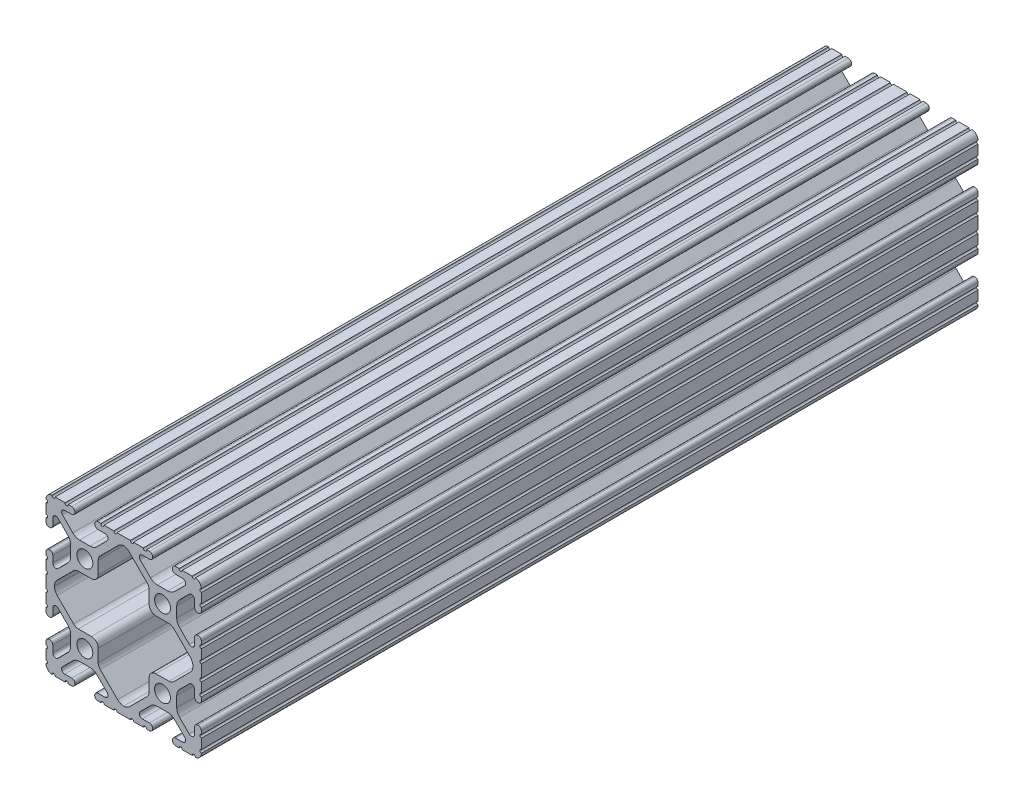
SolidWorks part; units mm, degrees
material "6061 Alloy"
ref_plane "Front Plane" through (0, 0, 0) normal (0, 0, 1) x (1, 0, 0)
ref_plane "Top Plane" through (0, 0, 0) normal (0, 1, 0) x (1, 0, 0)
ref_plane "Right Plane" through (0, 0, 0) normal (1, 0, 0) x (0, 0, -1)
sketch "Sketch1" plane through (0, 0, 0) normal (0, 0, 1) x (1, 0, 0)
  line L1 (-2.2101, -25.4) -> (2.2101, -25.4)
  line L2 (12.7883, 29.5847) -> (12.7883, -24.0404) construction
  line L3 (7.4579, -25.4) -> (8.4051, -25.4)
  line L4 (9.4615, -24.3587) -> (9.4615, -24.2315)
  line L5 (6.0878, -23.1902) -> (8.4051, -23.1902)
  line L6 (-12.7, -45.1098) -> (-12.7, 28.7522) construction
  line L7 (-25.8162, -12.7) -> (-12.7, -12.7) construction
  line L8 (0, 25.5922) -> (0, -25.5922) construction
  line L9 (-22.8238, 0) -> (0, 0) construction
  line L10 (8.763, -18.1257) -> (5.388, -21.5008)
  line L11 (14.3919, -17.1958) -> (11.0081, -17.1958)
  line L12 (20.012, -21.5008) -> (16.637, -18.1257)
  line L13 (16.9799, -23.1901) -> (19.2977, -23.1901)
  line L14 (15.9385, -24.3585) -> (15.9385, -24.2315)
  line L15 (16.9949, -25.4) -> (18.134, -25.4)
  line L16 (19.1384, -25.4) -> (20.1295, -25.4)
  line L17 (20.1295, -25.4) -> (22.4132, -25.4)
  line L18 (23.4501, -25.4) -> (23.4176, -25.4)
  line L19 (25.4, -23.294) -> (25.4, -23.2686)
  line L20 (25.4, -22.2526) -> (25.4, -21.1604)
  line L21 (25.4, -21.1604) -> (25.4, -19.0252)
  line L22 (25.4, -18.0092) -> (25.4, -16.916)
  line L23 (24.2316, -15.8746) -> (24.3586, -15.8746)
  line L24 (23.1902, -19.101) -> (23.1902, -16.916)
  line L25 (18.2781, -16.6418) -> (21.4558, -19.8194)
  line L26 (17.3482, -11.0035) -> (17.3482, -14.3967)
  line L27 (21.4566, -5.5875) -> (18.2808, -8.7557)
  line L28 (23.1902, -8.484) -> (23.1902, -6.3068)
  line L29 (-1.9878, -21.7759) -> (-7.684, -16.0797)
  line L30 (10.541, 8.1792) -> (14.8161, 8.1792)
  line L31 (-16.3772, -7.5334) -> (-21.7734, -2.1502)
  line L32 (24.3586, -9.5254) -> (24.2316, -9.5254)
  line L33 (25.4, -8.484) -> (25.4, -7.3277)
  line L34 (25.4, -3.0843) -> (25.4, -6.3117)
  line L35 (-25.4, 6.3117) -> (-25.4, 3.0843)
  line L36 (-22.6314, 0.0822) -> (-22.6314, -0.0822)
  line L37 (16.3772, -7.5334) -> (21.7734, -2.1502)
  line L38 (-14.8165, -8.1788) -> (-10.541, -8.1788)
  line L39 (12.7, -12.7) -> (25.8162, -12.7) construction
  line L40 (1.9878, -21.7759) -> (7.684, -16.0797)
  line L41 (3.2145, -25.4) -> (6.4535, -25.4)
  line L42 (22.6314, 0.0822) -> (22.6314, -0.0822)
  line L43 (-17.3482, -11.0035) -> (-17.3482, -14.3967)
  line L44 (25.4, 6.3117) -> (25.4, 3.0843)
  line L45 (-23.4501, -25.4) -> (-23.4176, -25.4)
  line L46 (-5.2705, 25.4) -> (-3.2145, 25.4)
  line L47 (-6.4535, 25.4) -> (-5.2705, 25.4)
  line L48 (-8.4051, 25.4) -> (-7.4579, 25.4)
  line L49 (-9.4615, 24.2315) -> (-9.4615, 24.3587)
  line L50 (-8.4051, 23.1902) -> (-6.0878, 23.1902)
  line L51 (-8.763, 18.1257) -> (-5.388, 21.5008)
  line L52 (-14.3919, 17.1958) -> (-11.0081, 17.1958)
  line L53 (-20.012, 21.5008) -> (-16.637, 18.1257)
  line L54 (-19.2977, 23.1901) -> (-16.9799, 23.1901)
  line L55 (-15.9385, 24.3585) -> (-15.9385, 24.2315)
  line L56 (-18.134, 25.4) -> (-16.9949, 25.4)
  line L57 (-20.1295, 25.4) -> (-19.1384, 25.4)
  line L58 (-22.4132, 25.4) -> (-20.1295, 25.4)
  line L59 (-23.4501, 25.4) -> (-23.4176, 25.4)
  line L60 (-25.4, 23.2686) -> (-25.4, 23.294)
  line L61 (-25.4, 21.1604) -> (-25.4, 22.2526)
  line L62 (-25.4, 19.0252) -> (-25.4, 21.1604)
  line L63 (-25.4, 16.916) -> (-25.4, 18.0092)
  line L64 (-24.3586, 15.8746) -> (-24.2316, 15.8746)
  line L65 (-23.1902, 19.101) -> (-23.1902, 16.916)
  line L66 (-18.2781, 16.6418) -> (-21.4558, 19.8194)
  line L67 (-17.3482, 11.0035) -> (-17.3482, 14.3967)
  line L68 (-21.4566, 5.5875) -> (-18.2808, 8.7557)
  line L69 (-23.1902, 6.3068) -> (-23.1902, 8.484)
  line L70 (-24.3586, 9.5254) -> (-24.2316, 9.5254)
  line L71 (-25.4, 7.3277) -> (-25.4, 8.484)
  line L74 (-14.8165, 8.1788) -> (-10.541, 8.1788)
  line L75 (-8.3312, 10.3886) -> (-8.3312, 14.5171)
  line L76 (3.2145, 25.4) -> (6.4535, 25.4)
  line L77 (1.7956, 21.9681) -> (7.684, 16.0797)
  line L78 (12.7, 12.7) -> (25.8162, 12.7) construction
  line L80 (16.3768, 7.5339) -> (21.7734, 2.1502)
  line L82 (25.4, 2.0683) -> (25.4, -2.0683)
  line L83 (8.3312, 12.7001) -> (8.3312, 10.389)
  line L84 (25.4, 7.3277) -> (25.4, 8.484)
  line L85 (24.3586, 9.5254) -> (24.2316, 9.5254)
  line L86 (-16.3772, 7.5334) -> (-21.7734, 2.1502)
  line L88 (-1.7956, 21.9681) -> (-7.684, 16.0797)
  line L89 (23.1902, 6.3068) -> (23.1902, 8.484)
  line L90 (21.4566, 5.5875) -> (18.2808, 8.7557)
  line L91 (17.3482, 11.0035) -> (17.3482, 14.3967)
  line L92 (18.2781, 16.6418) -> (21.4558, 19.8194)
  line L93 (23.1902, 19.101) -> (23.1902, 16.916)
  line L94 (24.2316, 15.8746) -> (24.3586, 15.8746)
  line L95 (25.4, 16.916) -> (25.4, 18.0092)
  line L96 (25.4, 19.0252) -> (25.4, 21.1604)
  line L97 (25.4, 21.1604) -> (25.4, 22.2526)
  line L98 (25.4, 23.2686) -> (25.4, 23.294)
  line L99 (23.4501, 25.4) -> (23.4176, 25.4)
  line L100 (20.1295, 25.4) -> (22.4132, 25.4)
  line L101 (19.1384, 25.4) -> (20.1295, 25.4)
  line L102 (16.9949, 25.4) -> (18.134, 25.4)
  line L103 (15.9385, 24.3585) -> (15.9385, 24.2315)
  line L104 (16.9799, 23.1901) -> (19.2977, 23.1901)
  line L105 (20.012, 21.5008) -> (16.637, 18.1257)
  line L106 (14.3919, 17.1958) -> (11.0081, 17.1958)
  line L107 (8.763, 18.1257) -> (5.388, 21.5008)
  line L108 (-25.8162, 12.7) -> (-12.7, 12.7) construction
  line L109 (6.0878, 23.1902) -> (8.4051, 23.1902)
  line L110 (9.4615, 24.2315) -> (9.4615, 24.3587)
  line L111 (7.4579, 25.4) -> (8.4051, 25.4)
  line L112 (8.3312, 12.7001) -> (8.3312, 14.5171)
  line L113 (-2.2101, 25.4) -> (2.2101, 25.4)
  line L114 (-22.4132, -25.4) -> (-20.1295, -25.4)
  line L115 (-20.1295, -25.4) -> (-19.1384, -25.4)
  line L116 (-18.134, -25.4) -> (-16.9949, -25.4)
  line L117 (-8.4051, -25.4) -> (-7.4579, -25.4)
  line L118 (-6.4535, -25.4) -> (-5.2705, -25.4)
  line L119 (-5.2705, -25.4) -> (-3.2145, -25.4)
  line L120 (-19.2977, -23.1901) -> (-16.9799, -23.1901)
  line L121 (-8.4051, -23.1902) -> (-6.0878, -23.1902)
  line L122 (-8.3312, -14.5171) -> (-8.3312, -10.3886)
  line L123 (-14.3919, -17.1958) -> (-11.0081, -17.1958)
  line L125 (-24.3586, -15.8746) -> (-24.2316, -15.8746)
  line L127 (-24.3586, -9.5254) -> (-24.2316, -9.5254)
  line L128 (14.8165, -8.1788) -> (10.541, -8.1788)
  line L129 (8.3312, -10.3886) -> (8.3312, -14.5171)
  line L130 (-9.4615, -24.3587) -> (-9.4615, -24.2315)
  line L132 (-15.9385, -24.3585) -> (-15.9385, -24.2315)
  line L134 (-25.4, -23.294) -> (-25.4, -23.2686)
  line L135 (-25.4, -22.2526) -> (-25.4, -21.1604)
  line L136 (-25.4, -21.1604) -> (-25.4, -19.0252)
  line L137 (-25.4, -18.0092) -> (-25.4, -16.916)
  line L138 (-25.4, -8.484) -> (-25.4, -7.3277)
  line L139 (-25.4, -6.3117) -> (-25.4, -4.1765)
  line L140 (-25.4, -4.1765) -> (-25.4, -3.0843)
  line L141 (-25.4, -2.0683) -> (-25.4, 2.0683)
  line L143 (-23.1902, -19.101) -> (-23.1902, -16.916)
  line L144 (-23.1902, -8.484) -> (-23.1902, -6.3068)
  line L198 (-21.4566, -5.5875) -> (-18.2808, -8.7557)
  line L200 (-18.2781, -16.6418) -> (-21.4558, -19.8194)
  line L213 (-20.012, -21.5008) -> (-16.637, -18.1257)
  line L215 (-8.763, -18.1257) -> (-5.388, -21.5008)
  arc A0 (6.4535, -25.4) -> (7.4579, -25.4) centre (6.9557, -25.3234) cw
  arc A1 (9.4615, -24.3587) -> (8.4051, -25.4) centre (8.4201, -24.3587) cw
  arc A2 (8.4051, -23.1902) -> (9.4615, -24.2315) centre (8.4201, -24.2315) cw
  arc A3 (6.0878, -23.1902) -> (5.388, -21.5008) centre (6.0878, -22.2006) cw
  arc A4 (8.763, -18.1257) -> (11.0081, -17.1958) centre (11.0081, -20.3708) cw
  arc A5 (14.3919, -17.1958) -> (16.637, -18.1257) centre (14.3919, -20.3708) cw
  arc A6 (20.012, -21.5008) -> (19.2977, -23.1901) centre (19.3122, -22.2006) cw
  arc A7 (15.9385, -24.2315) -> (16.9799, -23.1901) centre (16.9799, -24.2315) cw
  arc A8 (16.9949, -25.4) -> (15.9385, -24.3585) centre (16.9799, -24.3587) cw
  arc A9 (18.134, -25.4) -> (19.1384, -25.4) centre (18.6362, -25.3234) cw
  arc A10 (22.4132, -25.4) -> (23.4176, -25.4) centre (22.9154, -25.3234) cw
  arc A11 (25.4, -23.294) -> (23.4501, -25.4) centre (23.2918, -23.2977) cw
  arc A12 (25.4, -23.2686) -> (25.4, -22.2526) centre (25.4, -22.7606) cw
  arc A13 (25.4, -19.0252) -> (25.4, -18.0092) centre (25.4, -18.5172) cw
  arc A14 (24.3586, -15.8746) -> (25.4, -16.916) centre (24.3586, -16.916) cw
  arc A15 (23.1902, -16.916) -> (24.2316, -15.8746) centre (24.2316, -16.916) cw
  arc A16 (23.1902, -19.101) -> (21.4558, -19.8194) centre (22.1742, -19.101) cw
  arc A17 (18.2781, -16.6418) -> (17.3482, -14.3967) centre (20.5232, -14.3967) cw
  arc A18 (17.3482, -11.0035) -> (18.2808, -8.7557) centre (20.5232, -11.0035) cw
  arc A19 (0, -22.6304) -> (-1.9878, -21.7759) centre (0.0777, -19.7104) cw
  arc A20 (21.4566, -5.5875) -> (23.1902, -6.3068) centre (22.1742, -6.3068) cw
  arc A21 (24.2316, -9.5254) -> (23.1902, -8.484) centre (24.2316, -8.484) cw
  arc A22 (-14.8165, -8.1788) -> (-16.3772, -7.5334) centre (-14.8165, -5.969) cw
  arc A23 (-8.3312, -10.3886) -> (-10.541, -8.1788) centre (-10.541, -10.3886) ccw
  arc A24 (25.4, -8.484) -> (24.3586, -9.5254) centre (24.3586, -8.484) cw
  arc A25 (25.4, -7.3277) -> (25.4, -6.3117) centre (25.4, -6.8197) cw
  arc A26 (-22.6314, 0.0822) -> (-21.7734, 2.1502) centre (-19.7104, 0.0822) cw
  arc A27 (-7.684, -16.0797) -> (-8.3312, -14.5171) centre (-6.1214, -14.5171) cw
  arc A28 (-8.3312, 10.3886) -> (-10.541, 8.1788) centre (-10.541, 10.3886) cw
  circle A29 centre (12.7, -12.7) radius 2.6035
  arc A30 (14.8165, -8.1788) -> (16.3772, -7.5334) centre (14.8165, -5.969) ccw
  arc A31 (8.3312, -10.3886) -> (10.541, -8.1788) centre (10.541, -10.3886) cw
  arc A32 (8.3312, -14.5171) -> (7.684, -16.0797) centre (6.1214, -14.5171) cw
  arc A33 (0, -22.6304) -> (1.9878, -21.7759) centre (-0.0777, -19.7104) ccw
  arc A34 (2.2101, -25.4) -> (3.2145, -25.4) centre (2.7123, -25.3234) cw
  arc A35 (25.4, -3.0843) -> (25.4, -2.0683) centre (25.4, -2.5763) cw
  arc A36 (22.6314, 0.0822) -> (21.7734, 2.1502) centre (19.7104, 0.0822) ccw
  circle A37 centre (-12.7, -12.7) radius 2.6035
  arc A38 (-2.2101, 25.4) -> (-3.2145, 25.4) centre (-2.7123, 25.3234) cw
  arc A39 (-6.4535, 25.4) -> (-7.4579, 25.4) centre (-6.9557, 25.3234) cw
  arc A40 (-9.4615, 24.3587) -> (-8.4051, 25.4) centre (-8.4201, 24.3587) cw
  arc A41 (-8.4051, 23.1902) -> (-9.4615, 24.2315) centre (-8.4201, 24.2315) cw
  arc A42 (-6.0878, 23.1902) -> (-5.388, 21.5008) centre (-6.0878, 22.2006) cw
  arc A43 (-8.763, 18.1257) -> (-11.0081, 17.1958) centre (-11.0081, 20.3708) cw
  arc A44 (-14.3919, 17.1958) -> (-16.637, 18.1257) centre (-14.3919, 20.3708) cw
  arc A45 (-20.012, 21.5008) -> (-19.2977, 23.1901) centre (-19.3122, 22.2006) cw
  arc A46 (-15.9385, 24.2315) -> (-16.9799, 23.1901) centre (-16.9799, 24.2315) cw
  arc A47 (-16.9949, 25.4) -> (-15.9385, 24.3585) centre (-16.9799, 24.3587) cw
  arc A48 (-18.134, 25.4) -> (-19.1384, 25.4) centre (-18.6362, 25.3234) cw
  arc A49 (-22.4132, 25.4) -> (-23.4176, 25.4) centre (-22.9154, 25.3234) cw
  arc A50 (-25.4, 23.294) -> (-23.4501, 25.4) centre (-23.2918, 23.2977) cw
  arc A51 (-25.4, 23.2686) -> (-25.4, 22.2526) centre (-25.4, 22.7606) cw
  arc A52 (-25.4, 19.0252) -> (-25.4, 18.0092) centre (-25.4, 18.5172) cw
  arc A53 (-24.3586, 15.8746) -> (-25.4, 16.916) centre (-24.3586, 16.916) cw
  arc A54 (-23.1902, 16.916) -> (-24.2316, 15.8746) centre (-24.2316, 16.916) cw
  arc A55 (-23.1902, 19.101) -> (-21.4558, 19.8194) centre (-22.1742, 19.101) cw
  arc A56 (-18.2781, 16.6418) -> (-17.3482, 14.3967) centre (-20.5232, 14.3967) cw
  arc A57 (-17.3482, 11.0035) -> (-18.2808, 8.7557) centre (-20.5232, 11.0035) cw
  arc A58 (-21.4566, 5.5875) -> (-23.1902, 6.3068) centre (-22.1742, 6.3068) cw
  arc A59 (-24.2316, 9.5254) -> (-23.1902, 8.484) centre (-24.2316, 8.484) cw
  arc A60 (-25.4, 8.484) -> (-24.3586, 9.5254) centre (-24.3586, 8.484) cw
  arc A61 (-25.4, 7.3277) -> (-25.4, 6.3117) centre (-25.4, 6.8197) cw
  arc A62 (-25.4, 3.0843) -> (-25.4, 2.0683) centre (-25.4, 2.5763) cw
  circle A63 centre (-12.7, 12.7) radius 2.6035
  arc A64 (-8.3312, 14.5171) -> (-7.684, 16.0797) centre (-6.1214, 14.5171) cw
  arc A65 (2.2101, 25.4) -> (3.2145, 25.4) centre (2.7123, 25.3234) ccw
  arc A66 (0, 22.8111) -> (-1.7956, 21.9681) centre (0.2699, 19.9026) ccw
  arc A67 (8.3312, 14.5171) -> (7.684, 16.0797) centre (6.1214, 14.5171) ccw
  arc A68 (10.541, 8.1792) -> (8.3312, 10.389) centre (10.541, 10.389) cw
  arc A69 (14.8161, 8.1792) -> (16.3768, 7.5339) centre (14.8161, 5.9694) cw
  circle A70 centre (12.7, 12.7) radius 2.6035
  arc A71 (25.4, 3.0843) -> (25.4, 2.0683) centre (25.4, 2.5763) ccw
  arc A72 (-14.8165, 8.1788) -> (-16.3772, 7.5334) centre (-14.8165, 5.969) ccw
  arc A73 (25.4, 7.3277) -> (25.4, 6.3117) centre (25.4, 6.8197) ccw
  arc A74 (25.4, 8.484) -> (24.3586, 9.5254) centre (24.3586, 8.484) ccw
  arc A75 (22.6314, -0.0822) -> (21.7734, -2.1502) centre (19.7104, -0.0822) cw
  arc A76 (-22.6314, -0.0822) -> (-21.7734, -2.1502) centre (-19.7104, -0.0822) ccw
  arc A77 (24.2316, 9.5254) -> (23.1902, 8.484) centre (24.2316, 8.484) ccw
  arc A78 (21.4566, 5.5875) -> (23.1902, 6.3068) centre (22.1742, 6.3068) ccw
  arc A79 (1.7956, 21.9681) -> (0, 22.8111) centre (-0.2699, 19.9026) ccw
  arc A80 (17.3482, 11.0035) -> (18.2808, 8.7557) centre (20.5232, 11.0035) ccw
  arc A81 (18.2781, 16.6418) -> (17.3482, 14.3967) centre (20.5232, 14.3967) ccw
  arc A82 (23.1902, 19.101) -> (21.4558, 19.8194) centre (22.1742, 19.101) ccw
  arc A83 (23.1902, 16.916) -> (24.2316, 15.8746) centre (24.2316, 16.916) ccw
  arc A84 (24.3586, 15.8746) -> (25.4, 16.916) centre (24.3586, 16.916) ccw
  arc A85 (25.4, 19.0252) -> (25.4, 18.0092) centre (25.4, 18.5172) ccw
  arc A86 (25.4, 23.2686) -> (25.4, 22.2526) centre (25.4, 22.7606) ccw
  arc A87 (25.4, 23.294) -> (23.4501, 25.4) centre (23.2918, 23.2977) ccw
  arc A88 (22.4132, 25.4) -> (23.4176, 25.4) centre (22.9154, 25.3234) ccw
  arc A89 (18.134, 25.4) -> (19.1384, 25.4) centre (18.6362, 25.3234) ccw
  arc A90 (16.9949, 25.4) -> (15.9385, 24.3585) centre (16.9799, 24.3587) ccw
  arc A91 (15.9385, 24.2315) -> (16.9799, 23.1901) centre (16.9799, 24.2315) ccw
  arc A92 (20.012, 21.5008) -> (19.2977, 23.1901) centre (19.3122, 22.2006) ccw
  arc A93 (14.3919, 17.1958) -> (16.637, 18.1257) centre (14.3919, 20.3708) ccw
  arc A94 (8.763, 18.1257) -> (11.0081, 17.1958) centre (11.0081, 20.3708) ccw
  arc A95 (6.0878, 23.1902) -> (5.388, 21.5008) centre (6.0878, 22.2006) ccw
  arc A96 (8.4051, 23.1902) -> (9.4615, 24.2315) centre (8.4201, 24.2315) ccw
  arc A97 (9.4615, 24.3587) -> (8.4051, 25.4) centre (8.4201, 24.3587) ccw
  arc A98 (6.4535, 25.4) -> (7.4579, 25.4) centre (6.9557, 25.3234) ccw
  arc A182 (-25.4, -3.0843) -> (-25.4, -2.0683) centre (-25.4, -2.5763) ccw
  arc A183 (-25.4, -7.3277) -> (-25.4, -6.3117) centre (-25.4, -6.8197) ccw
  arc A184 (-25.4, -8.484) -> (-24.3586, -9.5254) centre (-24.3586, -8.484) ccw
  arc A185 (-24.2316, -9.5254) -> (-23.1902, -8.484) centre (-24.2316, -8.484) ccw
  arc A186 (-21.4566, -5.5875) -> (-23.1902, -6.3068) centre (-22.1742, -6.3068) ccw
  arc A187 (-17.3482, -11.0035) -> (-18.2808, -8.7557) centre (-20.5232, -11.0035) ccw
  arc A188 (-18.2781, -16.6418) -> (-17.3482, -14.3967) centre (-20.5232, -14.3967) ccw
  arc A189 (-23.1902, -19.101) -> (-21.4558, -19.8194) centre (-22.1742, -19.101) ccw
  arc A190 (-23.1902, -16.916) -> (-24.2316, -15.8746) centre (-24.2316, -16.916) ccw
  arc A191 (-24.3586, -15.8746) -> (-25.4, -16.916) centre (-24.3586, -16.916) ccw
  arc A192 (-25.4, -19.0252) -> (-25.4, -18.0092) centre (-25.4, -18.5172) ccw
  arc A193 (-25.4, -23.2686) -> (-25.4, -22.2526) centre (-25.4, -22.7606) ccw
  arc A194 (-25.4, -23.294) -> (-23.4501, -25.4) centre (-23.2918, -23.2977) ccw
  arc A195 (-22.4132, -25.4) -> (-23.4176, -25.4) centre (-22.9154, -25.3234) ccw
  arc A196 (-18.134, -25.4) -> (-19.1384, -25.4) centre (-18.6362, -25.3234) ccw
  arc A197 (-16.9949, -25.4) -> (-15.9385, -24.3585) centre (-16.9799, -24.3587) ccw
  arc A198 (-15.9385, -24.2315) -> (-16.9799, -23.1901) centre (-16.9799, -24.2315) ccw
  arc A199 (-20.012, -21.5008) -> (-19.2977, -23.1901) centre (-19.3122, -22.2006) ccw
  arc A200 (-14.3919, -17.1958) -> (-16.637, -18.1257) centre (-14.3919, -20.3708) ccw
  arc A201 (-8.763, -18.1257) -> (-11.0081, -17.1958) centre (-11.0081, -20.3708) ccw
  arc A202 (-6.0878, -23.1902) -> (-5.388, -21.5008) centre (-6.0878, -22.2006) ccw
  arc A203 (-8.4051, -23.1902) -> (-9.4615, -24.2315) centre (-8.4201, -24.2315) ccw
  arc A204 (-9.4615, -24.3587) -> (-8.4051, -25.4) centre (-8.4201, -24.3587) ccw
  arc A205 (-6.4535, -25.4) -> (-7.4579, -25.4) centre (-6.9557, -25.3234) ccw
  arc A206 (-2.2101, -25.4) -> (-3.2145, -25.4) centre (-2.7123, -25.3234) ccw
  point P397 (16.6343, 7.277)
  dimension "D1" = 5.207
  dimension "D3" = 6.477
  dimension "D4" = 8.2042
  dimension "D5" = 25.4
  dimension "D10" = 12.7
  dimension "D8" = 2.2098
  dimension "D9" = 2.2098
  dimension "D12" = 2.2098
  dimension "D13" = 2.2098
  dimension "D14" = 2.2098
  dimension "D15" = 2.2098
  dimension "D16" = 2.921
  dimension "D17" = 2.921
  dimension "D18" = 2.921
  dimension "D19" = 2.921
  dimension "D20" = 2.921
  dimension "D21" = 2.921
  dimension "D2" = 2.2098
  dimension "D6" = 14.859
  dimension "D7" = 50.8
  dimension "D11" = 2.2098
extrude "Extrude1" add sketch "Sketch1" against normal blind 254
